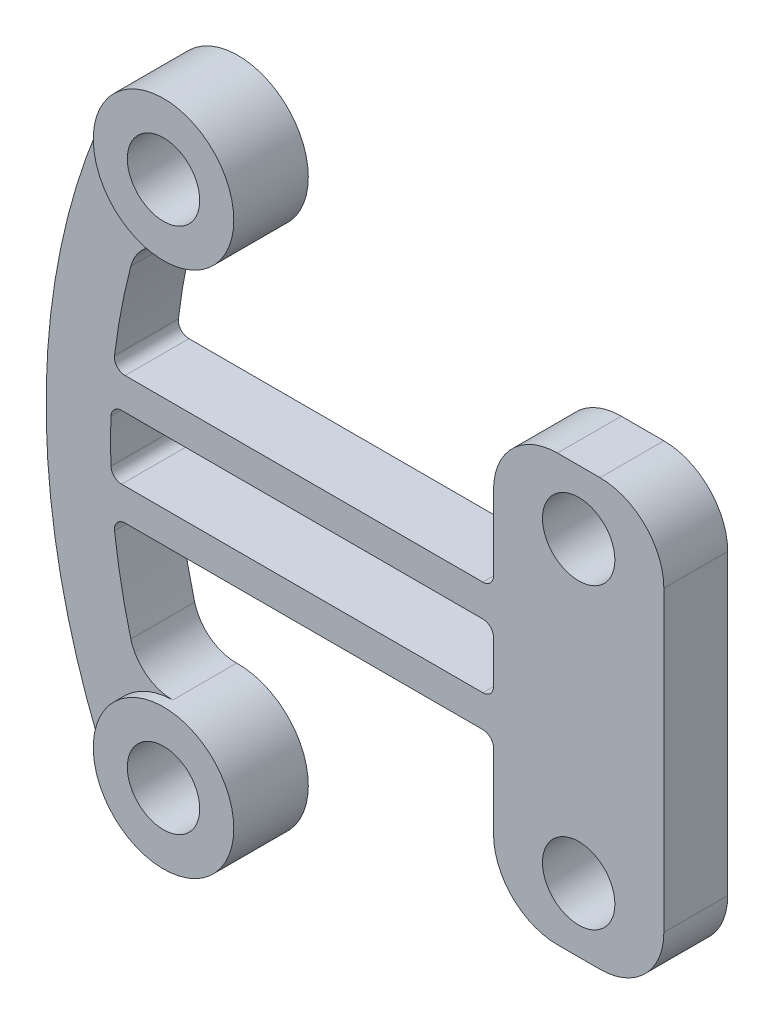
SolidWorks part; units mm, degrees
ref_plane "Front Plane" through (0, 0, 0) normal (0, 0, 1) x (1, 0, 0)
ref_plane "Top Plane" through (0, 0, 0) normal (0, 1, 0) x (1, 0, 0)
ref_plane "Right Plane" through (0, 0, 0) normal (1, 0, 0) x (0, 0, -1)
ref_plane "Plane1" through (0, 0, 0) normal (0, 0, -1) x (-1, 0, 0)
sketch "Sketch1" plane through (0, 0, 0) normal (0, 0, -1) x (-1, 0, 0)
  line L0 (-16, 3) -> (-16, -3)
  line L1 (-16, -3) -> (9.8641, -3)
  line L2 (9.8641, 3) -> (-16, 3)
  arc A0 (9.8641, -3) -> (8.4873, -9.4291) centre (-19.8438, 0) cw
  arc A1 (8.4873, -9.4291) -> (9.997, -13.7566) centre (7, -12.375) ccw
  arc A2 (9.997, -13.7566) -> (9.997, 13.7566) centre (-19.8438, 0) ccw
  arc A3 (9.997, 13.7566) -> (8.4873, 9.4291) centre (7, 12.375) ccw
  arc A4 (8.4873, 9.4291) -> (9.8641, 3) centre (-19.8438, 0) cw
extrude "Boss-Extrude1" add sketch "Sketch1" against normal blind 3
sketch "Sketch2" plane through (0, -3, 0) normal (0, -1, 0) x (1, 0, 0)
  line L0 (8, 3) -> (16, 3)
  line L1 (16, 3) -> (16, 0)
  line L2 (16, 0) -> (8, 0)
  line L3 (8, 0) -> (8, 3)
extrude "Boss-Extrude2" add sketch "Sketch2" along normal blind 7
sketch "Sketch3" plane through (0, 3, 0) normal (0, 1, 0) x (-1, 0, 0)
  line L0 (-16, 3) -> (-8, 3)
  line L1 (-8, 3) -> (-8, 0)
  line L2 (-8, 0) -> (-16, 0)
  line L3 (-16, 0) -> (-16, 3)
extrude "Boss-Extrude3" add sketch "Sketch3" along normal blind 7
sketch "Sketch4" plane through (0, 0, 3) normal (0, 0, 1) x (1, 0, 0)
  circle A0 centre (-7, 12.375) radius 3.3001
extrude "Boss-Extrude4" add sketch "Sketch4" along normal blind 0.5
sketch "Sketch5" plane through (0, 0, 3) normal (0, 0, 1) x (1, 0, 0)
  circle A0 centre (-7, -12.375) radius 3.3001
extrude "Boss-Extrude5" add sketch "Sketch5" along normal blind 0.5
sketch "Sketch6" plane through (0, 0, 3) normal (0, 0, 1) x (1, 0, 0)
  line L0 (8, 1.5) -> (-9.9482, 1.5)
  line L1 (-9.9482, -1.5) -> (8, -1.5)
  line L2 (8, -1.5) -> (8, 1.5)
  line L3 (8, -3) -> (-9.8641, -3) construction
  arc A0 (-9.9482, 1.5) -> (-9.9482, -1.5) centre (19.8732, 0) ccw
  dimension "D1" = 3
  dimension "D2" = 17.9482
  dimension "D3" = 1.5
extrude "Cut-Extrude1" cut sketch "Sketch6" against normal through all
hole_wizard "M3 Clearance Hole2" positions "Sketch8" profile "Sketch7" hole size "M3" standard "ANSI Metric" end condition through all
sketch "Sketch8" plane through (0, 0, 0) normal (0, 0, -1) x (-1, 0, 0)
  line L0 (-16, 10) -> (-8, 10) construction
  line L1 (-8, -10) -> (-16, -10) construction
  point P0 (-12, -7)
  point P1 (-12, 7)
  dimension "D1" = 3
  dimension "D2" = 3
sketch "Sketch7" plane through (12, -7, 0) normal (1, 0, 0) x (0, 1, 0)
  line L0 (0, 0) -> (0, 3.5)
  line L1 (0, 3.5) -> (1.7, 3.5)
  line L2 (1.7, 3.5) -> (1.7, 0)
  line L5 (1.7, 0) -> (0, 0)
  line L11 (0, -6.35) -> (0, 107.95) construction
  dimension "Thru Hole Dia." = 3.4
  dimension "Thru Hole Depth" = 3.5
hole_wizard "M3 Clearance Hole1" positions "Sketch10" profile "Sketch9" hole size "M3" standard "ANSI Metric" end condition through all
sketch "Sketch10" plane through (0, 0, 0) normal (0, 0, -1) x (-1, 0, 0)
  point P0 (7, 12.375)
  point P1 (7, -12.375)
sketch "Sketch9" plane through (-7, 12.375, 0) normal (1, 0, 0) x (0, 1, 0)
  line L0 (0, 0) -> (0, 3.5)
  line L1 (0, 3.5) -> (1.7, 3.5)
  line L2 (1.7, 3.5) -> (1.7, 0)
  line L5 (1.7, 0) -> (0, 0)
  line L11 (0, -6.35) -> (0, 107.95) construction
  dimension "Thru Hole Dia." = 3.4
  dimension "Thru Hole Depth" = 3.5
fillet "Fillet1" radius 0.5 8 edges at (8, 3, 1.5) (8, -3, 1.5) (-9.8641, 3, 1.5) (-9.9482, -1.5, 1.5) (8, 1.5, 1.5) (-9.9482, 1.5, 1.5) (-9.8641, -3, 1.5) (8, -1.5, 1.5)
fillet "Fillet2" radius 2 2 edges at (-8.4873, -9.4291, 1.5) (-8.4873, 9.4291, 1.5)
fillet "Fillet3" radius 3 4 edges at (16, -10, 1.5) (8, -10, 1.5) (16, 10, 1.5) (8, 10, 1.5)
